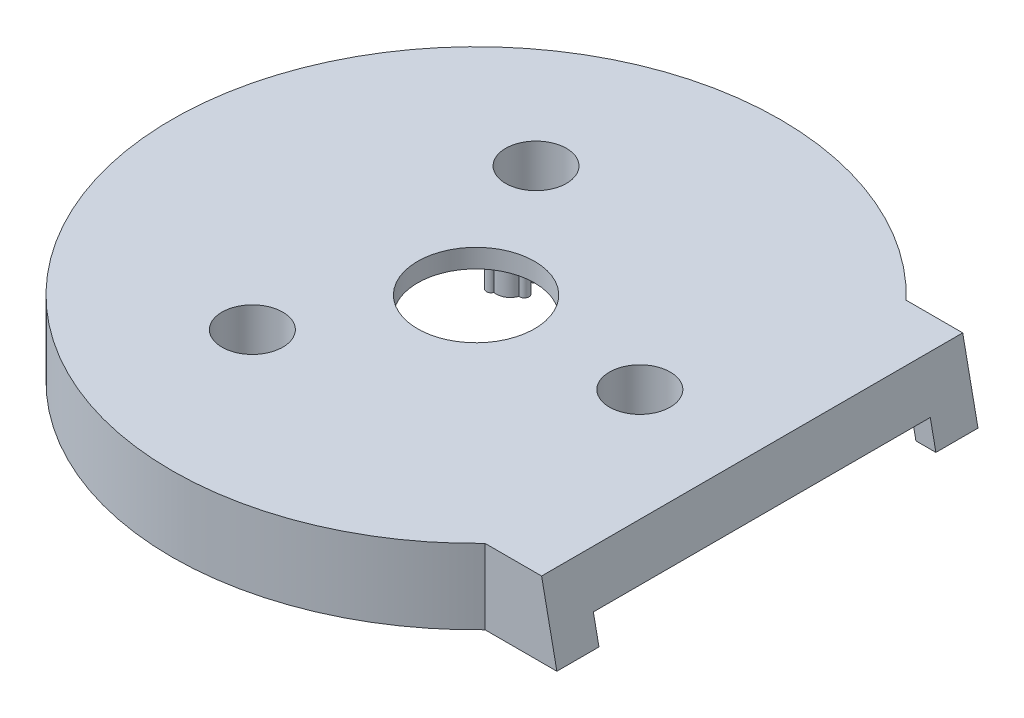
SolidWorks part; units mm, degrees
material "ABS"
ref_plane "Front Plane" through (0, 0, 0) normal (0, 0, 1) x (1, 0, 0)
ref_plane "Top Plane" through (0, 0, 0) normal (0, 1, 0) x (1, 0, 0)
ref_plane "Right Plane" through (0, 0, 0) normal (1, 0, 0) x (0, 0, -1)
sketch "Sketch1" plane through (0, 0, 0) normal (0, 1, 0) x (1, 0, 0)
  line L0 (25, 44.9998) -> (69, 44.9998)
  line L1 (25, 44.9998) -> (25, -45.0002)
  line L2 (25, -45.0002) -> (69, -45.0002)
  line L3 (69, 44.9998) -> (69, -45.0002)
  circle A0 centre (0, 0) radius 65
  dimension "D1" = 130
  dimension "D2" = 90
  dimension "D3" = 51.478
  dimension "D4" = 25
  dimension "D5" = 51.4783
  dimension "D6" = 69
extrude "Boss-Extrude1" add sketch "Sketch1" along normal blind 16 contours L0 A0 L2 L1 | A0 L2 L3 L0 | L2 A0 L0 L1
sketch "Sketch3" plane through (0, 0, 0) normal (0, -1, 0) x (1, 0, 0)
  line L0 (46.904, 45.0002) -> (69, 45.0002) construction
  line L1 (64, 40.2002) -> (13.6488, 40.2002)
  line L2 (64, 40.2002) -> (64, -40.1998)
  line L3 (64, -40.1998) -> (13.6488, -40.1998)
  line L4 (13.6488, 40.2002) -> (13.6488, -40.1998)
  line L5 (46.9043, -44.9998) -> (69, -44.9998) construction
  line L6 (69, -44.9998) -> (69, 45.0002) construction
  circle A1 centre (0, 0) radius 60
  dimension "D1" = 120
  dimension "D2" = 4.8
  dimension "D3" = 4.8
  dimension "D4" = 5
extrude "Cut-Extrude1" cut sketch "Sketch3" against normal blind 12
sketch "Sketch4" plane through (69, 0, 0) normal (1, 0, 0) x (0, 0, -1)
  line L0 (44.9998, 0) -> (-45.0002, 0) construction
  line L1 (-36.0002, 5) -> (35.9998, 5)
  line L2 (-36.0002, 5) -> (-36.0002, 0)
  line L3 (-36.0002, 0) -> (35.9998, 0)
  line L4 (35.9998, 5) -> (35.9998, 0)
  line L5 (-45.0002, 16) -> (-45.0002, 0) construction
  dimension "D1" = 72
  dimension "D2" = 5
  dimension "D3" = 9
extrude "Cut-Extrude2" cut sketch "Sketch4" against normal blind 16
sketch "Sketch8" plane through (0, 12, 0) normal (0, -1, 0) x (1, 0, 0)
  circle A1 centre (44.5415, 40.2002) radius 1.5
  circle A4 centre (-25.2123, 54.4458) radius 3.5
  circle A5 centre (-25, -54.5436) radius 3.5
  circle A6 centre (44.5415, 40.2002) radius 3.5
  circle A7 centre (44.5418, -40.1998) radius 3.5
  circle A8 centre (-25.2123, 54.4458) radius 1.5
  circle A9 centre (-25, -54.5436) radius 1.5
  circle A10 centre (44.5418, -40.1998) radius 1.5
  circle A11 centre (0, 0) radius 60
  dimension "D1" = 3
  dimension "D2" = 60
  dimension "D3" = 7
  dimension "D4" = 7
  dimension "D5" = 7
  dimension "D6" = 3
  dimension "D7" = 3
  dimension "D8" = 3
  dimension "D12" = 120
  dimension "D9" = 60
  dimension "D10" = 7
  dimension "D11" = 108.9895
  dimension "D13" = 25
extrude "InternalHolesBody" add sketch "Sketch8" along normal blind 12
sketch "Sketch13" plane through (0, 12, 0) normal (0, -1, 0) x (1, 0, 0)
  circle A0 centre (44.5415, 40.2002) radius 1.5
  circle A1 centre (-25.2123, 54.4458) radius 1.5
  circle A3 centre (-25, -54.5436) radius 1.5
  circle A5 centre (44.5418, -40.1998) radius 1.5
  arc A6 (-26.3557, -53.9016) -> (-23.6287, -55.1515) centre (0, 0) ccw construction
  arc A7 (-23.8434, 55.059) -> (-26.5654, 53.7985) centre (0, 0) ccw construction
extrude "InternalHolesCut" cut sketch "Sketch13" along normal blind 12
sketch "Sketch14" plane through (0, 0, -44.9998) normal (0, 0, -1) x (-1, 0, 0)
  line L0 (-46.9043, 16) -> (-69, 16) construction
  line L1 (-69, 16) -> (-59, 16)
  line L2 (-69, 16) -> (-69, -33)
  line L5 (-59, 16) -> (-69, -33)
  line L6 (-69, 16) -> (-69, 0) construction
  dimension "D1" = 10
  dimension "D2" = 49
sketch "Sketch15" plane through (0, 0, 45.0002) normal (0, 0, 1) x (1, 0, 0)
  line L0 (69, 16) -> (69, 0) construction
  line L1 (69, 16) -> (54.7644, 16)
  line L2 (69, 16) -> (69, 0)
  line L3 (69, 0) -> (54.7644, 0)
  line L4 (54.7644, 16) -> (54.7644, 0)
  line L5 (46.904, 0) -> (69, 0) construction
  dimension "D1" = 14.2356
extrude "InternalBodyExtension" add sketch "Sketch15" against normal blind 90
extrude "ExternalDiagonalCut" cut sketch "Sketch14" against normal blind 90
sketch "Sketch17" plane through (0, 0, 45.0002) normal (0, 0, 1) x (1, 0, 0)
  line L8 (58, 0) -> (54.7347, 0)
  line L11 (54.7347, 0) -> (54.7347, 12)
  line L12 (55.551, 12) -> (58, 0)
  line L13 (54.7347, 12) -> (55.551, 12)
  dimension "D1" = 4.2653
  dimension "D2" = 12
extrude "DiagonalCut" cut sketch "Sketch17" against normal blind 80.4 from offset 4.8 offset against normal yes
sketch "Sketch19" plane through (59.7757, 12.1991, 0) normal (0.9798, 0.2, 0) x (0, 0, -1)
  line L0 (44.9998, -12.4506) -> (-45.0002, -12.4506) construction
  line L1 (-36.0002, -12.4506) -> (35.9998, -12.4506)
  line L2 (-36.0002, -12.4506) -> (-36.0002, -6.4506)
  line L3 (-36.0002, -6.4506) -> (35.9998, -6.4506)
  line L4 (35.9998, -12.4506) -> (35.9998, -6.4506)
  line L5 (-45.0002, -12.4506) -> (-45.0002, 3.8792) construction
  dimension "D1" = 9
  dimension "D2" = 72
  dimension "D3" = 6
extrude "DisplayCut" cut sketch "Sketch19" against normal blind 8.4
sketch "Sketch26" plane through (0, 12, 0) normal (0, -1, 0) x (1, 0, 0)
  arc A2 (-20.1364, 22.7578) -> (-9.6406, 28.8175) centre (-17.5, 30.3109) ccw
  arc A3 (-22.723, -24.2512) -> (-22.723, -36.3706) centre (-17.5, -30.3109) ccw
  arc A4 (42.8594, 1.4934) -> (32.3636, 7.5531) centre (35, 0) ccw
  circle A5 centre (35, 0) radius 6.5
  circle A6 centre (-17.5, -30.3109) radius 6.5
  circle A7 centre (-17.5, 30.3109) radius 6.5
  arc A9 (-9.6406, 28.8175) -> (-9.6406, 31.8043) centre (-9.5, 30.3109) ccw
  arc A10 (-20.1364, 37.864) -> (-22.723, 36.3706) centre (-21.5, 37.2391) ccw
  arc A11 (-22.723, 24.2512) -> (-20.1364, 22.7578) centre (-21.5, 23.3827) ccw
  arc A12 (-9.6406, -31.8043) -> (-9.6406, -28.8175) centre (-9.5, -30.3109) ccw
  arc A17 (42.8594, -1.4934) -> (42.8594, 1.4934) centre (43, 0) ccw
  arc A19 (32.3636, 7.5531) -> (29.777, 6.0597) centre (31, 6.9282) ccw
  arc A20 (-9.6406, 31.8043) -> (-20.1364, 37.864) centre (-17.5, 30.3109) ccw
  arc A21 (-22.723, 36.3706) -> (-22.723, 24.2512) centre (-17.5, 30.3109) ccw
  arc A23 (-9.6406, -28.8175) -> (-20.1364, -22.7578) centre (-17.5, -30.3109) ccw
  arc A24 (-22.723, -36.3706) -> (-20.1364, -37.864) centre (-21.5, -37.2391) ccw
  arc A25 (-20.1364, -37.864) -> (-9.6406, -31.8043) centre (-17.5, -30.3109) ccw
  arc A26 (-20.1364, -22.7578) -> (-22.723, -24.2512) centre (-21.5, -23.3827) ccw
  arc A30 (29.777, -6.0597) -> (32.3636, -7.5531) centre (31, -6.9282) ccw
  arc A31 (32.3636, -7.5531) -> (42.8594, -1.4934) centre (35, 0) ccw
  arc A32 (29.777, 6.0597) -> (29.777, -6.0597) centre (35, 0) ccw
  dimension "D2" = 16
  dimension "D3" = 16
  dimension "D4" = 16
  dimension "D5" = 13
  dimension "D6" = 13
  dimension "D7" = 13
  dimension "D8" = 3
  dimension "D9" = 3
  dimension "D10" = 3
  dimension "D15" = 3
  dimension "D17" = 3
  dimension "D19" = 3
  dimension "D11" = 13.8564
  dimension "D12" = 13.8564
  dimension "D13" = 13.8564
  dimension "D20" = 13.8564
  dimension "D21" = 13.8564
  dimension "D22" = 13.8564
  dimension "D23" = 13.8564
  dimension "D24" = 13.8564
  dimension "D25" = 13.8564
  dimension "D26" = 60.6218
  dimension "D27" = 60.6218
  dimension "D28" = 60.6218
extrude "Boss-Extrude2" add sketch "Sketch26" along normal blind 11
sketch "Sketch27" plane through (0, 12, 0) normal (0, -1, 0) x (1, 0, 0)
  circle A1 centre (-17.5, 30.3109) radius 6.5
  circle A2 centre (35, 0) radius 6.5
  circle A3 centre (-17.5, -30.3109) radius 6.5
  dimension "D1" = 13
  dimension "D2" = 13
  dimension "D3" = 13
extrude "Cut-Extrude3" cut sketch "Sketch27" against normal through all
sketch "Sketch28" plane through (0, 1, 0) normal (0, -1, 0) x (1, 0, 0)
  circle A0 centre (-17.5, 30.3109) radius 8
  dimension "D1" = 16
extrude "Boss-Extrude3" add sketch "Sketch28" against normal blind 2 and the other way blind 1
sketch "Sketch30" plane through (0, 0, 0) normal (0, -1, 0) x (1, 0, 0)
  circle A0 centre (-17.5, 30.3109) radius 1.5
  dimension "D1" = 3
extrude "Cut-Extrude4" cut sketch "Sketch30" against normal blind 3
sketch "Sketch31" plane through (0, 1, 0) normal (0, -1, 0) x (1, 0, 0)
  circle A0 centre (35, 0) radius 8
  circle A1 centre (35, 0) radius 1.5
  dimension "D1" = 16
  dimension "D2" = 3
extrude "Boss-Extrude4" add sketch "Sketch31" against normal blind 2 and the other way blind 1
sketch "Sketch32" plane through (0, 1, 0) normal (0, -1, 0) x (1, 0, 0)
  circle A0 centre (-17.5, -30.3109) radius 8
  circle A1 centre (-17.5, -30.3109) radius 1.5
  dimension "D1" = 16
  dimension "D2" = 3
extrude "Boss-Extrude5" add sketch "Sketch32" against normal blind 2 and the other way blind 1
sketch "Sketch33" plane through (0, 12, 0) normal (0, -1, 0) x (1, 0, 0)
  circle A0 centre (0, 0) radius 12.5
  dimension "D1" = 25
sketch "Sketch34" plane through (0, 12, 0) normal (0, -1, 0) x (1, 0, 0)
  arc A2 (-12.2706, 19.2812) -> (-12.2706, 15.3598) centre (-10, 17.3205) ccw
  arc A3 (-12.2706, -15.3598) -> (-12.2706, -19.2812) centre (-10, -17.3205) ccw
  arc A4 (17.7294, 1.9607) -> (17.7294, -1.9607) centre (20, 0) ccw
  arc A6 (-7.1667, 16.3345) -> (-7.1667, 18.3065) centre (-7, 17.3205) ccw
  circle A7 centre (-10, 17.3205) radius 1.5
  arc A8 (-10.5628, 20.2673) -> (-12.2706, 19.2812) centre (-11.5, 19.9186) ccw
  arc A9 (-12.2706, 15.3598) -> (-10.5628, 14.3738) centre (-11.5, 14.7224) ccw
  circle A10 centre (-10, -17.3205) radius 1.5
  arc A12 (-7.1667, -18.3065) -> (-7.1667, -16.3345) centre (-7, -17.3205) ccw
  arc A13 (-12.2706, -19.2812) -> (-10.5628, -20.2673) centre (-11.5, -19.9186) ccw
  arc A14 (-10.5628, -14.3738) -> (-12.2706, -15.3598) centre (-11.5, -14.7224) ccw
  circle A16 centre (20, 0) radius 1.5
  arc A17 (22.8333, -0.986) -> (22.8333, 0.986) centre (23, 0) ccw
  arc A18 (17.7294, -1.9607) -> (19.4372, -2.9467) centre (18.5, -2.5981) ccw
  arc A19 (19.4372, 2.9467) -> (17.7294, 1.9607) centre (18.5, 2.5981) ccw
  arc A20 (19.4372, -2.9467) -> (22.8333, -0.986) centre (20, 0) ccw
  arc A21 (22.8333, 0.986) -> (19.4372, 2.9467) centre (20, 0) ccw
  arc A22 (-10.5628, 14.3738) -> (-7.1667, 16.3345) centre (-10, 17.3205) ccw
  arc A23 (-7.1667, -16.3345) -> (-10.5628, -14.3738) centre (-10, -17.3205) ccw
  arc A24 (-7.1667, 18.3065) -> (-10.5628, 20.2673) centre (-10, 17.3205) ccw
  arc A25 (-10.5628, -20.2673) -> (-7.1667, -18.3065) centre (-10, -17.3205) ccw
  dimension "D2" = 6
  dimension "D3" = 6
  dimension "D4" = 6
  dimension "D8" = 3
  dimension "D12" = 2
  dimension "D13" = 2
  dimension "D14" = 2
  dimension "D15" = 3
  dimension "D16" = 2
  dimension "D17" = 2
  dimension "D18" = 2
  dimension "D22" = 2
  dimension "D23" = 2
  dimension "D24" = 2
  dimension "D25" = 3
  dimension "D5" = 34.641
  dimension "D6" = 34.641
  dimension "D7" = 34.641
  dimension "D9" = 5.1962
  dimension "D10" = 5.1962
  dimension "D11" = 5.1962
  dimension "D19" = 5.1962
  dimension "D20" = 5.1962
  dimension "D21" = 5.1962
  dimension "D26" = 5.1962
  dimension "D27" = 5.1962
  dimension "D28" = 5.1962
extrude "Boss-Extrude6" add sketch "Sketch34" along normal blind 8
extrude "Cut-Extrude5" cut sketch "Sketch33" against normal through all
sketch "Sketch35" plane through (0, 12, 0) normal (0, -1, 0) x (1, 0, 0)
  circle A0 centre (20, 0) radius 2
  circle A1 centre (-10, -17.3205) radius 2
  circle A2 centre (-10, 17.3205) radius 2
  dimension "D1" = 4
  dimension "D2" = 4
  dimension "D3" = 4
extrude "Boss-Extrude7" add sketch "Sketch35" along normal blind 3
